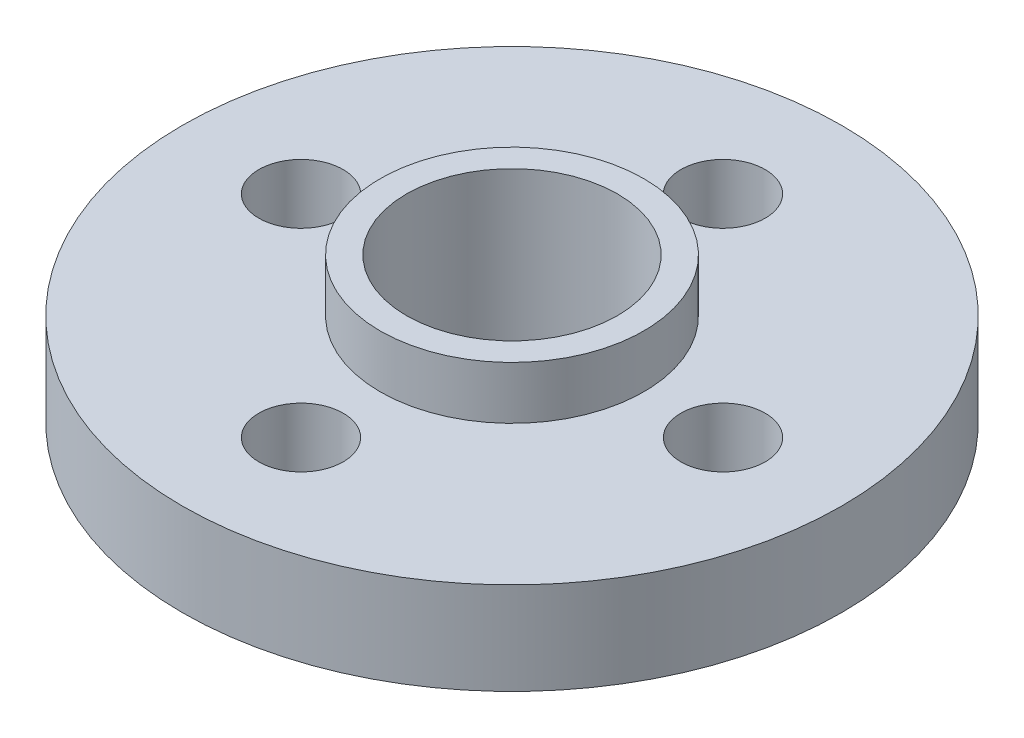
SolidWorks part; units mm, degrees
ref_plane "Front Plane" through (0, 0, 0) normal (0, 0, 1) x (1, 0, 0)
ref_plane "Top Plane" through (0, 0, 0) normal (0, 1, 0) x (1, 0, 0)
ref_plane "Right Plane" through (0, 0, 0) normal (1, 0, 0) x (0, 0, -1)
sketch "Sketch2" plane through (0, 0, 0) normal (0, 1, 0) x (1, 0, 0)
  circle A0 centre (0, 0) radius 12.5
  circle A1 centre (0, 0) radius 4
  dimension "D1" = 25
  dimension "D2" = 8
extrude "Boss-Extrude1" add sketch "Sketch2" along normal blind 3.5
sketch "Sketch3" plane through (0, 3.5, 0) normal (0, 1, 0) x (1, 0, 0)
  circle A0 centre (0, 0) radius 4
  circle A1 centre (0, 0) radius 5
  circle A2 centre (0, 0) radius 4 construction
  dimension "D1" = 10
extrude "Boss-Extrude2" add sketch "Sketch3" along normal blind 2
sketch "Sketch4" plane through (0, 0, 0) normal (0, -1, 0) x (1, 0, 0)
  circle A0 centre (0, 0) radius 4
  circle A1 centre (0, 0) radius 5
  circle A2 centre (0, 0) radius 4 construction
  dimension "D1" = 10
extrude "Boss-Extrude3" add sketch "Sketch4" along normal blind 5
sketch "Sketch5" plane through (0, 3.5, 0) normal (0, 1, 0) x (1, 0, 0)
  circle A0 centre (0, 8) radius 1.6
  circle A1 centre (8, 0) radius 1.6
  circle A2 centre (0, -8) radius 1.6
  circle A3 centre (-8, 0) radius 1.6
  point P12 (0, 0)
  dimension "D2" = 3.2
  dimension "D1" = 8
  dimension "D3" = 4
extrude "Cut-Extrude1" cut sketch "Sketch5" against normal through all
